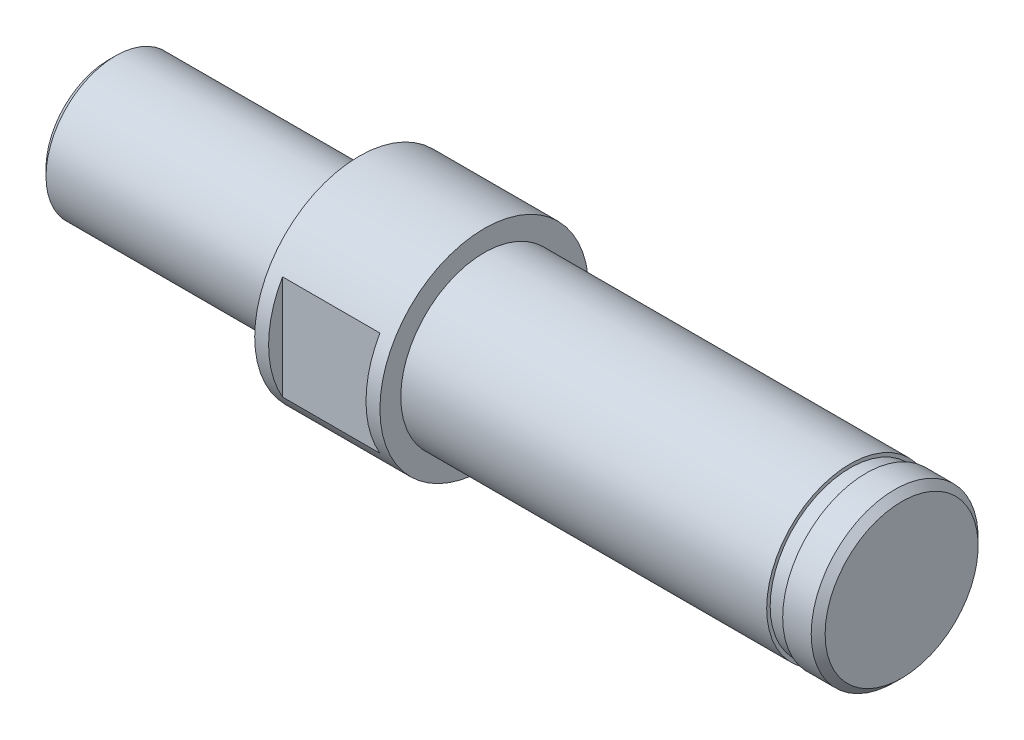
SolidWorks part; units mm, degrees
ref_plane "Front" through (0, 0, 0) normal (0, 0, 1) x (1, 0, 0)
ref_plane "Top" through (0, 0, 0) normal (0, 1, 0) x (1, 0, 0)
ref_plane "Right" through (0, 0, 0) normal (1, 0, 0) x (0, 0, -1)
sketch "Sketch1" plane through (0, 0, 0) normal (0, 0, 1) x (1, 0, 0)
  line L0 (-21.9806, 0) -> (42.7374, 0) construction
  line L1 (-18, 0) -> (-18, 5)
  line L2 (-18, 5) -> (0, 5)
  line L3 (0, 5) -> (0, 7.5)
  line L4 (0, 7.5) -> (9, 7.5)
  line L5 (9, 7.5) -> (9, 6)
  line L6 (9, 6) -> (39, 6)
  line L7 (39, 6) -> (39, 0)
  line L8 (-18, 0) -> (39, 0)
  dimension "D1" = 18
  dimension "D2" = 9
  dimension "D3" = 39
  dimension "D4" = 10
  dimension "D5" = 15
  dimension "D6" = 12
revolve "Revolve1" add sketch "Sketch1" angle 360 about L0
cosmetic thread "Cosmetic Thread1" parameters "D1"=17, "D2"=8.5
sketch "Sketch3" plane through (0, 0, 0) normal (0, 0, 1) x (1, 0, 0)
  line L0 (-19.4038, 0) -> (46.1326, 0) construction
  line L1 (39, 6) -> (9, 6) construction
  line L2 (36.45, 6) -> (35.3, 6)
  line L3 (36.45, 6) -> (36.45, 5.75)
  line L4 (36.45, 5.75) -> (35.3, 5.75)
  line L5 (35.3, 6) -> (35.3, 5.75)
  line L6 (0, 7.5) -> (0, -7.5) construction
  dimension "D1" = 11.5
  dimension "D2" = 1.15
  dimension "D3" = 35.3
revolve "Cut-Revolve1" cut sketch "Sketch3" angle 360 about L0
ref_plane "Plane1" through (1, 0, 0) normal (-1, 0, 0) x (0, 0, 1)
sketch "Sketch2" plane through (1, 0, 0) normal (1, 0, 0) x (0, 0, -1)
  line L0 (0, -8.599) -> (0, 8.5592) construction
  line L2 (6.5, -7.5) -> (-6.5, -7.5)
  line L3 (6.5, -7.5) -> (6.5, 7.5)
  line L4 (6.5, 7.5) -> (-6.5, 7.5)
  line L5 (-6.5, -7.5) -> (-6.5, 7.5)
  circle A0 centre (0, 0) radius 7.5 construction
  dimension "D1" = 13
extrude "Cut-Extrude1" cut sketch "Sketch2" along normal blind 7 flip side to cut
chamfer "Chamfer1" distance 0.5 2 edges at (39, 0, 6) (-18, 0, 5)
